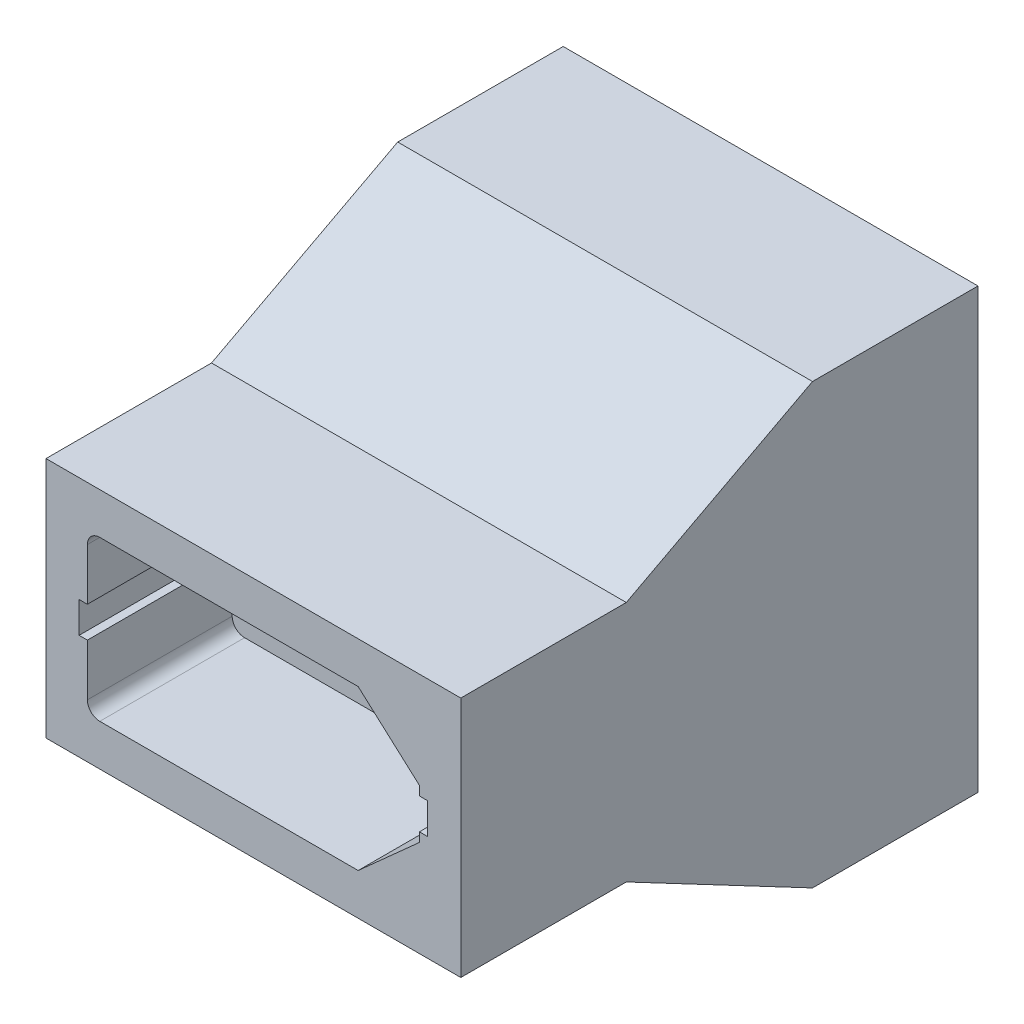
SolidWorks part; units mm, degrees
material "PET"
ref_plane "Front Plane" through (0, 0, 0) normal (0, 0, 1) x (1, 0, 0)
ref_plane "Top Plane" through (0, 0, 0) normal (0, 1, 0) x (1, 0, 0)
ref_plane "Right Plane" through (0, 0, 0) normal (1, 0, 0) x (0, 0, -1)
sketch "Sketch1" plane through (0, 0, 0) normal (0, 0, 1) x (1, 0, 0)
  line L18 (6.5133, 3.85) -> (-5.975, 3.85)
  line L19 (-6.575, 3.25) -> (-6.575, -3.25)
  line L20 (-5.975, -3.85) -> (6.5133, -3.85)
  line L21 (6.5133, -3.85) -> (9.475, -1.1947)
  line L22 (9.475, -1.1947) -> (9.475, 1.1947)
  line L23 (9.475, 1.1947) -> (6.5133, 3.85)
  line L24 (6.5133, 3.85) -> (-5.975, 3.85)
  line L25 (-6.575, 3.25) -> (-6.575, -3.25)
  line L26 (-5.975, -3.85) -> (6.5133, -3.85)
  line L27 (6.5133, -3.85) -> (9.475, -1.1947)
  line L28 (9.475, -1.1947) -> (9.475, 1.1947)
  line L29 (9.475, 1.1947) -> (6.5133, 3.85)
  line L30 (0.2691, -3.85) -> (0.2691, 13.35) construction
  line L31 (9.475, 0) -> (-6.575, 0) construction
  line L32 (11.475, 15.35) -> (-8.575, 15.35)
  line L33 (11.475, 15.35) -> (11.475, -5.85)
  line L34 (11.475, -5.85) -> (-8.575, -5.85)
  line L35 (-8.575, 15.35) -> (-8.575, -5.85)
  line L36 (6.5133, 13.35) -> (-5.975, 13.35)
  line L37 (-6.575, 12.75) -> (-6.575, 6.25)
  line L38 (-5.975, 5.65) -> (6.5133, 5.65)
  line L39 (6.5133, 5.65) -> (9.475, 8.3053)
  line L40 (9.475, 8.3053) -> (9.475, 10.6947)
  line L41 (9.475, 10.6947) -> (6.5133, 13.35)
  line L42 (6.5133, 13.35) -> (-5.975, 13.35)
  line L43 (-6.575, 12.75) -> (-6.575, 6.25)
  line L44 (-5.975, 5.65) -> (6.5133, 5.65)
  line L45 (6.5133, 5.65) -> (9.475, 8.3053)
  line L46 (9.475, 8.3053) -> (9.475, 10.6947)
  line L47 (9.475, 10.6947) -> (6.5133, 13.35)
  line L48 (11.475, 15.35) -> (-8.575, -5.85) construction
  line L49 (11.475, -5.85) -> (-8.575, 15.35) construction
  line L50 (9.725, 9.025) -> (9.725, 9.975) construction
  line L51 (9.475, 10.25) -> (9.875, 10.25)
  line L52 (9.475, 10.25) -> (9.475, 8.75)
  line L53 (9.475, 8.75) -> (9.875, 8.75)
  line L54 (9.875, 10.25) -> (9.875, 8.75)
  line L55 (-6.575, 10.25) -> (-6.975, 10.25)
  line L56 (-6.575, 10.25) -> (-6.575, 8.75)
  line L57 (-6.575, 8.75) -> (-6.975, 8.75)
  line L58 (-6.975, 10.25) -> (-6.975, 8.75)
  line L59 (-6.825, 9.3) -> (-6.825, 9.7) construction
  line L61 (9.475, 0.75) -> (9.875, 0.75)
  line L62 (9.875, -0.75) -> (9.875, 0.75)
  line L63 (9.475, -0.75) -> (9.875, -0.75)
  line L64 (9.475, -0.75) -> (9.475, 0.75)
  line L65 (-6.575, 0.75) -> (-6.975, 0.75)
  line L66 (-6.975, -0.75) -> (-6.975, 0.75)
  line L67 (-6.575, -0.75) -> (-6.975, -0.75)
  line L68 (-6.575, -0.75) -> (-6.575, 0.75)
  arc A6 (-5.975, 3.85) -> (-6.575, 3.25) centre (-5.975, 3.25) ccw
  arc A7 (-6.575, -3.25) -> (-5.975, -3.85) centre (-5.975, -3.25) ccw
  arc A8 (-5.975, 3.85) -> (-6.575, 3.25) centre (-5.975, 3.25) ccw
  arc A9 (-6.575, -3.25) -> (-5.975, -3.85) centre (-5.975, -3.25) ccw
  arc A12 (-5.975, 13.35) -> (-6.575, 12.75) centre (-5.975, 12.75) ccw
  arc A13 (-6.575, 6.25) -> (-5.975, 5.65) centre (-5.975, 6.25) ccw
  arc A14 (-5.975, 13.35) -> (-6.575, 12.75) centre (-5.975, 12.75) ccw
  arc A15 (-6.575, 6.25) -> (-5.975, 5.65) centre (-5.975, 6.25) ccw
  point P2 (1.45, 4.75)
  point P7 (0.2691, 4.75)
  point P12 (1.45, 0)
  point P35 (9.875, 9.5)
  point P42 (9.725, 9.5)
  point P43 (-6.975, 9.5)
  point P46 (-6.825, 9.5)
  point P50 (1.45, 4.75)
  dimension "D3" = 0
  dimension "D4" = 2
  dimension "D5" = 0
  dimension "D6" = 2
  dimension "D7" = 1.5
  dimension "D8" = 0
  dimension "D9" = 0.4
  dimension "D10" = 1.5
  dimension "D11" = 0.4
  dimension "D12" = 0
  dimension "D1" = 0.1
  dimension "D2" = 0.1
extrude "Boss-Extrude1" add sketch "Sketch1" against normal blind 7 contours L32 L35 L34 L33 A15 L43 L57 L58 L55 A14 L42 L47 L46 L51 L54 L53 L45 L44 A9 L25 L67 L66 L65 A8 L24 L29 L28 L61 L62 L63 L27 L26
sketch "Sketch2" plane through (0, 0, 0) normal (0, 0, 1) x (1, 0, 0)
  line L16 (6.0924, 2.75) -> (-5.475, 2.75)
  line L17 (-5.475, 2.75) -> (-5.475, -2.75)
  line L18 (-5.475, -2.75) -> (6.0924, -2.75)
  line L19 (6.0924, -2.75) -> (8.375, -0.7035)
  line L20 (8.375, -0.7035) -> (8.375, 0.7035)
  line L21 (8.375, 0.7035) -> (6.0924, 2.75)
  line L22 (6.0924, 2.75) -> (-5.475, 2.75)
  line L23 (-5.475, 2.75) -> (-5.475, -2.75)
  line L24 (-5.475, -2.75) -> (6.0924, -2.75)
  line L25 (6.0924, -2.75) -> (8.375, -0.7035)
  line L26 (8.375, -0.7035) -> (8.375, 0.7035)
  line L27 (8.375, 0.7035) -> (6.0924, 2.75)
  line L34 (6.0924, 12.25) -> (-5.475, 12.25)
  line L35 (-5.475, 12.25) -> (-5.475, 6.75)
  line L36 (-5.475, 6.75) -> (6.0924, 6.75)
  line L37 (6.0924, 6.75) -> (8.375, 8.7965)
  line L38 (8.375, 8.7965) -> (8.375, 10.2035)
  line L39 (8.375, 10.2035) -> (6.0924, 12.25)
  line L40 (6.0924, 12.25) -> (-5.475, 12.25)
  line L41 (-5.475, 12.25) -> (-5.475, 6.75)
  line L42 (-5.475, 6.75) -> (6.0924, 6.75)
  line L43 (6.0924, 6.75) -> (8.375, 8.7965)
  line L44 (8.375, 8.7965) -> (8.375, 10.2035)
  line L45 (8.375, 10.2035) -> (6.0924, 12.25)
  line L48 (11.475, 15.35) -> (-8.575, 15.35)
  line L49 (-8.575, 15.35) -> (-8.575, -5.85)
  line L50 (-8.575, -5.85) -> (11.475, -5.85)
  line L51 (11.475, -5.85) -> (11.475, 15.35)
  line L52 (11.475, 15.35) -> (-8.575, 15.35)
  line L53 (-8.575, 15.35) -> (-8.575, -5.85)
  line L54 (-8.575, -5.85) -> (11.475, -5.85)
  line L55 (11.475, -5.85) -> (11.475, 15.35)
  dimension "D1" = 1
  dimension "D2" = 1
  dimension "D3" = 0
extrude "Boss-Extrude2" add sketch "Sketch2" along normal blind 1
sketch "Sketch3" plane through (0, 0, 11) normal (0, 0, -1) x (-1, 0, 0)
  line L6 (6.825, 4.95) -> (6.825, 4.55) construction
  line L7 (6.575, 4) -> (6.975, 4)
  line L8 (6.575, 4) -> (6.575, 5.5)
  line L9 (6.575, 5.5) -> (6.975, 5.5)
  line L10 (6.975, 4) -> (6.975, 5.5)
  line L11 (6.575, 4.75) -> (-9.475, 4.75) construction
  line L12 (-6.5133, 0.9) -> (5.975, 0.9)
  line L13 (6.575, 1.5) -> (6.575, 8)
  line L14 (5.975, 8.6) -> (-6.5133, 8.6)
  line L15 (-6.5133, 8.6) -> (-9.475, 5.9447)
  line L16 (-9.475, 5.9447) -> (-9.475, 3.5553)
  line L17 (-9.475, 3.5553) -> (-6.5133, 0.9)
  line L18 (-6.5133, 0.9) -> (5.975, 0.9)
  line L19 (6.575, 1.5) -> (6.575, 8)
  line L20 (5.975, 8.6) -> (-6.5133, 8.6)
  line L21 (-6.5133, 8.6) -> (-9.475, 5.9447)
  line L22 (-9.475, 5.9447) -> (-9.475, 3.5553)
  line L23 (-9.475, 3.5553) -> (-6.5133, 0.9)
  line L24 (-1.45, 4.75) -> (-1.45, 0.9) construction
  line L25 (-9.475, 5.5) -> (-9.875, 5.5)
  line L26 (-9.875, 4) -> (-9.875, 5.5)
  line L27 (-9.475, 4) -> (-9.875, 4)
  line L28 (-9.475, 4) -> (-9.475, 5.5)
  line L30 (8.575, 10.6) -> (-11.475, 10.6)
  line L31 (8.575, 10.6) -> (8.575, -1.1)
  line L32 (8.575, -1.1) -> (-11.475, -1.1)
  line L33 (-11.475, 10.6) -> (-11.475, -1.1)
  line L34 (8.575, 10.6) -> (-11.475, -1.1) construction
  line L35 (8.575, -1.1) -> (-11.475, 10.6) construction
  arc A4 (5.975, 0.9) -> (6.575, 1.5) centre (5.975, 1.5) ccw
  arc A5 (6.575, 8) -> (5.975, 8.6) centre (5.975, 8) ccw
  arc A6 (5.975, 0.9) -> (6.575, 1.5) centre (5.975, 1.5) ccw
  arc A7 (6.575, 8) -> (5.975, 8.6) centre (5.975, 8) ccw
  point P4 (6.975, 4.75)
  point P7 (6.825, 4.75)
  dimension "D2" = 0
  dimension "D3" = 0.4
  dimension "D4" = 1.5
  dimension "D5" = 2
  dimension "D6" = 2
  dimension "D7" = 2
  dimension "D8" = 2
  dimension "D1" = 0.1
extrude "Boss-Extrude3" add sketch "Sketch3" against normal blind 7 separate body contours L30 L33 L32 L31 A7 L19 L9 L10 L7 A6 L18 L23 L22 L27 L26 L25 L21 L20
sketch "Sketch4" plane through (0, 0, 11) normal (0, 0, -1) x (-1, 0, 0)
  line L12 (-6.0924, 2) -> (5.475, 2)
  line L13 (5.475, 2) -> (5.475, 7.5)
  line L14 (5.475, 7.5) -> (-6.0924, 7.5)
  line L15 (-6.0924, 7.5) -> (-8.375, 5.4535)
  line L16 (-8.375, 5.4535) -> (-8.375, 4.0465)
  line L17 (-8.375, 4.0465) -> (-6.0924, 2)
  line L18 (-6.0924, 2) -> (5.475, 2)
  line L19 (5.475, 2) -> (5.475, 7.5)
  line L20 (5.475, 7.5) -> (-6.0924, 7.5)
  line L21 (-6.0924, 7.5) -> (-8.375, 5.4535)
  line L22 (-8.375, 5.4535) -> (-8.375, 4.0465)
  line L23 (-8.375, 4.0465) -> (-6.0924, 2)
  line L26 (8.575, 10.6) -> (-11.475, 10.6)
  line L27 (-11.475, 10.6) -> (-11.475, -1.1)
  line L28 (-11.475, -1.1) -> (8.575, -1.1)
  line L29 (8.575, -1.1) -> (8.575, 10.6)
  line L30 (8.575, 10.6) -> (-11.475, 10.6)
  line L31 (-11.475, 10.6) -> (-11.475, -1.1)
  line L32 (-11.475, -1.1) -> (8.575, -1.1)
  line L33 (8.575, -1.1) -> (8.575, 10.6)
  dimension "D1" = 1
  dimension "D2" = 0
extrude "Boss-Extrude4" add sketch "Sketch4" along normal blind 1
sketch "Sketch5" plane through (11.475, 0, 0) normal (1, 0, 0) x (0, 0, -1)
  line L0 (-1, -5.85) -> (-10, -1.1)
  line L1 (-1, 15.35) -> (-10, 10.6)
  line L2 (-1, -5.85) -> (-1, 15.35)
  line L3 (-10, -1.1) -> (-10, 10.6)
  line L4 (-1, -4.85) -> (-10, -0.1)
  line L5 (-1, 14.35) -> (-10, 9.6)
  line M8 (-10, -1.1) -> (-10, 10.6)
  dimension "D1" = 0
  dimension "D2" = 0
  dimension "D3" = 1
  dimension "D4" = 1
extrude "Boss-Extrude5" add sketch "Sketch5" against normal up to surface (20.05 mm away) contours L2 L4 L0 M8 | L5 L2 L1 M8 up to face at (-8.575, 4.75, 14)
sketch "Sketch6" plane through (11.475, 0, 0) normal (1, 0, 0) x (0, 0, -1)
  line L8 (-1, -5.85) -> (-1, 15.35)
  line L9 (-10, 10.6) -> (-10, -1.1)
  line L16 (7, 15.35) -> (-1, 15.35)
  line L17 (-1, 15.35) -> (-10, 10.6)
  line L18 (-10, 10.6) -> (-18, 10.6)
  line L19 (-18, 10.6) -> (-18, -1.1)
  line L20 (-18, -1.1) -> (-10, -1.1)
  line L21 (-10, -1.1) -> (-1, -5.85)
  line L22 (-1, -5.85) -> (7, -5.85)
  line L23 (7, -5.85) -> (7, 15.35)
  line L24 (7, 15.35) -> (-1, 15.35)
  line L25 (-1, 15.35) -> (-10, 10.6)
  line L26 (-10, 10.6) -> (-18, 10.6)
  line L27 (-18, 10.6) -> (-18, -1.1)
  line L28 (-18, -1.1) -> (-10, -1.1)
  line L29 (-10, -1.1) -> (-1, -5.85)
  line L30 (-1, -5.85) -> (7, -5.85)
  line L31 (7, -5.85) -> (7, 15.35)
  line M17 (-10, 9.6) -> (-1, 14.35)
  line M18 (-1, 14.35) -> (-1, -4.85)
  line M19 (-1, -4.85) -> (-10, -0.1)
  line M20 (-10, -0.1) -> (-10, 9.6)
  dimension "D1" = 0
extrude "Boss-Extrude6" add sketch "Sketch6" against normal blind 1 contours M17 M20 M19 M18
sketch "Sketch7" plane through (-8.575, 0, 0) normal (-1, 0, 0) x (0, 0, 1)
  line L8 (10, -1.1) -> (10, 10.6)
  line L9 (1, 15.35) -> (1, -5.85)
  line L16 (-7, -5.85) -> (1, -5.85)
  line L17 (1, -5.85) -> (10, -1.1)
  line L18 (10, -1.1) -> (18, -1.1)
  line L19 (18, -1.1) -> (18, 10.6)
  line L20 (18, 10.6) -> (10, 10.6)
  line L21 (10, 10.6) -> (1, 15.35)
  line L22 (1, 15.35) -> (-7, 15.35)
  line L23 (-7, 15.35) -> (-7, -5.85)
  line L24 (-7, -5.85) -> (1, -5.85)
  line L25 (1, -5.85) -> (10, -1.1)
  line L26 (10, -1.1) -> (18, -1.1)
  line L27 (18, -1.1) -> (18, 10.6)
  line L28 (18, 10.6) -> (10, 10.6)
  line L29 (10, 10.6) -> (1, 15.35)
  line L30 (1, 15.35) -> (-7, 15.35)
  line L31 (-7, 15.35) -> (-7, -5.85)
  line M9 (1, -4.85) -> (1, 14.35)
  line M10 (1, 14.35) -> (10, 9.6)
  line M11 (10, 9.6) -> (10, -0.1)
  line M12 (10, -0.1) -> (1, -4.85)
  dimension "D1" = 0
extrude "Boss-Extrude7" add sketch "Sketch7" against normal blind 1 contours M9 M12 M11 M10
